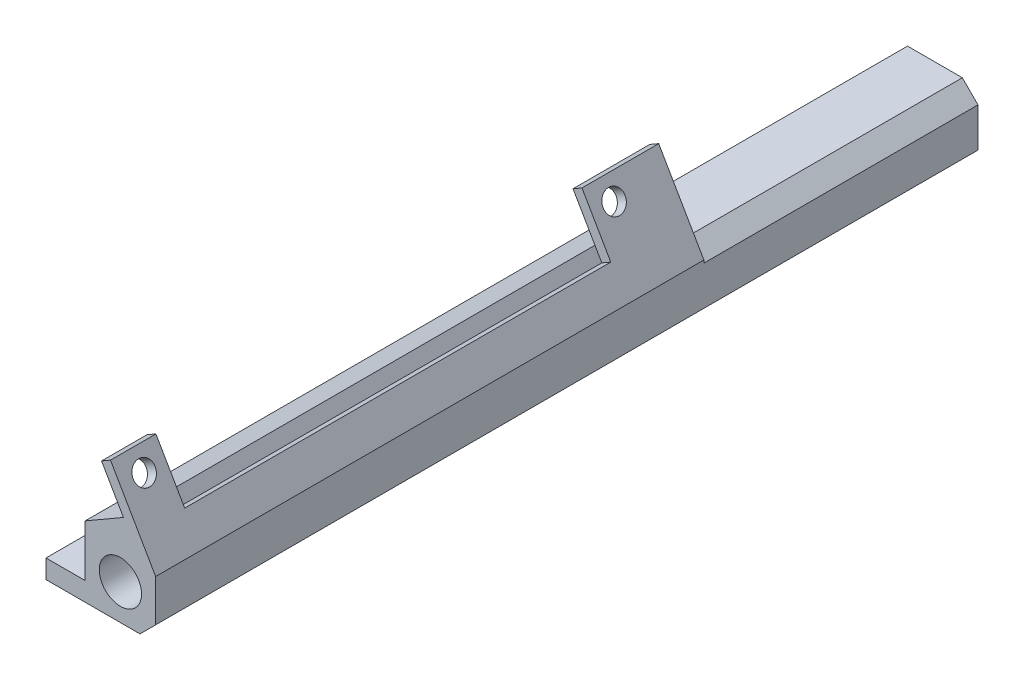
SolidWorks part; units mm, degrees
other "Markup1"
sketch "Sketch18" plane through (59.69, 0, 0) normal (0, 0, 1) x (1, 0, 0)
sketch "Sketch20" plane through (59.69, 0, 0) normal (0, 0, 1) x (1, 0, 0)
sketch "Sketch23" plane through (59.69, 0, 0) normal (0, 0, 1) x (1, 0, 0)
other "Markup2"
sketch "Sketch19" plane through (59.69, 0, 0) normal (0, 0, 1) x (1, 0, 0)
sketch "Sketch21" plane through (59.69, 0, 0) normal (0, 0, 1) x (1, 0, 0)
sketch "Sketch24" plane through (59.69, 0, 0) normal (0, 0, 1) x (1, 0, 0)
ref_plane "Front Plane" through (0, 0, 0) normal (0, 0, 1) x (1, 0, 0)
ref_plane "Top Plane" through (0, 0, 0) normal (0, 1, 0) x (1, 0, 0)
ref_plane "Right Plane" through (0, 0, 0) normal (1, 0, 0) x (0, 0, -1)
sketch "Sketch1" plane through (0, 0, 0) normal (0, 1, 0) x (1, 0, 0)
  line L1 (0, 0) -> (77.47, 0)
  line L2 (0, 0) -> (0, 133.35)
  line L3 (0, 133.35) -> (77.47, 133.35)
  line L4 (77.47, 0) -> (77.47, 133.35)
  dimension "D1" = 77.47
  dimension "D2" = 133.35
extrude "Boss-Extrude1" add sketch "Sketch1" along normal blind 11.43
sketch "Sketch2" plane through (0, 0, 0) normal (0, 0, 1) x (1, 0, 0)
  line L0 (5.715, 5.715) -> (71.755, 5.715) construction
  line L1 (38.735, 11.43) -> (38.735, 0) construction
  line L2 (0, 11.43) -> (77.47, 11.43) construction
  line L3 (0, 0) -> (77.47, 0) construction
  circle A0 centre (5.715, 5.715) radius 3.429
  circle A1 centre (71.755, 5.715) radius 3.429
  point P10 (38.735, 5.715)
  dimension "D1" = 6.858
  dimension "D2" = 66.04
extrude "Cut-Extrude1" cut sketch "Sketch2" against normal through all
sketch "Sketch3" plane through (0, 11.43, 0) normal (0, 1, 0) x (1, 0, 0)
  line L0 (11.43, 133.35) -> (11.43, 95.25)
  line L1 (77.47, 133.35) -> (0, 133.35) construction
  line L2 (11.43, 133.35) -> (66.04, 133.35)
  line L3 (66.04, 133.35) -> (66.04, 95.25)
  line L4 (53.34, 82.55) -> (24.13, 82.55)
  line L5 (0, 133.35) -> (0, 0) construction
  arc A0 (66.04, 95.25) -> (53.34, 82.55) centre (53.34, 95.25) cw
  arc A1 (24.13, 82.55) -> (11.43, 95.25) centre (24.13, 95.25) cw
  point P10 (38.735, 133.35)
  dimension "D1" = 12.7
  dimension "D2" = 11.43
  dimension "D3" = 50.8
extrude "Cut-Extrude2" cut sketch "Sketch3" against normal through all
sketch "Sketch4" plane through (0, 0, -133.35) normal (0, 0, -1) x (-1, 0, 0)
  line L0 (-11.43, 0) -> (-11.43, 11.43) construction
  line L1 (-66.04, 11.43) -> (-11.43, 11.43)
  line L2 (-66.04, 11.43) -> (-66.04, 5.08)
  line L3 (-66.04, 5.08) -> (-11.43, 5.08)
  line L4 (-11.43, 11.43) -> (-11.43, 5.08)
  line L5 (-11.43, 0) -> (0, 0) construction
  dimension "D1" = 5.08
extrude "Cut-Extrude3" cut sketch "Sketch4" against normal through all
chamfer "Chamfer1" distance 2.54 angle 45 4 edges at (0, 0, -66.675) (0, 11.43, -66.675) (77.47, 0, -66.675) (77.47, 11.43, -66.675)
sketch "Sketch5" plane through (0, 11.43, 0) normal (0, 1, 0) x (1, 0, 0)
  line L0 (66.04, 82.55) -> (0, 82.55)
  line L1 (66.04, 0) -> (66.04, 95.25) construction
  line L2 (0, 0) -> (0, 133.35) construction
  line L3 (0, 82.55) -> (0, 133.35)
  line L4 (0, 133.35) -> (66.04, 133.35)
  line L5 (66.04, 133.35) -> (66.04, 82.55)
  line L6 (24.13, 82.55) -> (53.34, 82.55) construction
extrude "Cut-Extrude4" cut sketch "Sketch5" against normal through all
sketch "Sketch6" plane through (0, 11.43, 0) normal (0, 1, 0) x (1, 0, 0)
  line L0 (53.34, 82.55) -> (53.34, 0)
  line L1 (11.43, 82.55) -> (66.04, 82.55) construction
  line L2 (66.04, 0) -> (11.43, 0) construction
  line L3 (53.34, 0) -> (0, 0)
  line L4 (0, 0) -> (0, 82.55)
  line L5 (0, 82.55) -> (53.34, 82.55)
  line L6 (66.04, 0) -> (66.04, 133.35) construction
  dimension "D1" = 12.7
extrude "Cut-Extrude5" cut sketch "Sketch6" against normal through all
sketch "Sketch7" plane through (0, 5.08, 0) normal (0, 1, 0) x (1, 0, 0)
  line L0 (53.34, 82.55) -> (66.04, 82.55) construction
  line L1 (66.04, 0) -> (66.04, 82.55) construction
  circle A0 centre (62.23, 74.93) radius 1.778
  circle A4 centre (62.23, 13.97) radius 1.778
  dimension "D1" = 3.556
  dimension "D2" = 7.62
  dimension "D3" = 68.58
  dimension "D4" = 3.81
extrude "Hole Cuts 1" cut sketch "Sketch7" against normal through all
sketch "Sketch8" plane through (0, 0, 0) normal (0, 0, 1) x (1, 0, 0)
  line L0 (77.47, 11.8699) -> (77.47, 8.89)
  line L1 (77.47, 11.8699) -> (71.882, 21.5486)
  line L2 (71.882, 21.5486) -> (68.6183, 19.6643)
  line L3 (68.6183, 19.6643) -> (71.5393, 14.605)
  line L4 (71.5393, 14.605) -> (66.04, 11.43)
  line L5 (77.47, 11.43) -> (68.58, 11.43) construction
  line L6 (66.04, 11.43) -> (74.93, 11.43) construction
  line L7 (66.04, 11.43) -> (74.93, 11.43)
  line L9 (77.47, 8.89) -> (77.47, 2.54) construction
  line L10 (74.93, 11.43) -> (77.47, 8.89)
  dimension "D2" = 11.176
  dimension "D3" = 6.35
  dimension "D4" = 5.842
  dimension "D6" = 60
extrude "Boss-Extrude2" add sketch "Sketch8" against normal blind 88.9
sketch "Sketch9" plane through (0, 0, 0) normal (0, 0, 1) x (1, 0, 0)
  line L0 (74.93, 0) -> (66.04, 0) construction
  line L1 (53.34, 0) -> (74.93, 0) construction
  line L3 (66.04, 0) -> (59.69, 0) construction
  line L4 (59.69, 0) -> (53.34, 0)
  line L5 (53.34, 0) -> (53.34, 5.08)
  line L6 (53.34, 5.08) -> (59.69, 5.08)
  line L7 (66.04, 5.08) -> (53.34, 5.08) construction
  line L8 (59.69, 5.08) -> (59.69, 0)
  dimension "D1" = 6.35
extrude "Cut-Extrude7" cut sketch "Sketch9" against normal up to next
sketch "Sketch10" plane through (0, 0, 0) normal (0, 0, 1) x (1, 0, 0)
  line L0 (59.69, 5.08) -> (66.04, 5.08)
  line L1 (66.04, 5.08) -> (66.04, 3.81)
  line L2 (66.04, 3.81) -> (59.69, 3.81)
  line L3 (59.69, 0) -> (59.69, 5.08) construction
  line L4 (59.69, 3.81) -> (59.69, 5.08)
  line L5 (59.69, 0) -> (74.93, 0) construction
  dimension "D1" = 3.81
extrude "Cut-Extrude8" cut sketch "Sketch10" against normal up to next
sketch "Sketch11" plane through (59.9786, 34.6287, 0) normal (-0.866, -0.5, 0) x (0, 0, 1)
  line L0 (-88.9, -23.1213) -> (0, -23.1213) construction
  line L2 (0, -17.2793) -> (0, -23.1213) construction
  circle A0 centre (-3.81, -19.3113) radius 1.778
  circle A1 centre (-80.01, -19.3113) radius 1.778
  dimension "D1" = 3.556
  dimension "D4" = 76.2
  dimension "D3" = 3.81
  dimension "D2" = 3.81
extrude "Hole Cuts 2" cut sketch "Sketch11" against normal up to next
sketch "Sketch12" plane through (63.2423, 36.513, 0) normal (0.866, 0.5, 0) x (0, 0, -1)
  line L1 (88.9, -17.2793) -> (0, -17.2793)
  line L2 (88.9, -17.2793) -> (88.9, -28.4553)
  line L3 (88.9, -28.4553) -> (0, -28.4553)
  line L4 (0, -17.2793) -> (0, -28.4553)
extrude "Cut-Extrude10" cut sketch "Sketch12" against normal blind 1.27
sketch "Sketch22" plane through (0, 0, 0) normal (0, 0, 1) x (1, 0, 0)
  line L0 (-928.245, 5.715) -> (49071.755, 5.715) construction
  line L1 (71.755, 5.715) -> (64.2465, 18.7201) construction
  line L2 (64.9306, 17.5352) -> (69.33, 20.0752)
  line L3 (64.9306, 17.5352) -> (67.8516, 12.4759)
  line L4 (69.33, 20.0752) -> (72.251, 15.0159)
  line L5 (67.8516, 12.4759) -> (72.251, 15.0159)
  line L6 (70.7821, 20.9136) -> (68.6183, 19.6643) construction
  line L7 (71.5393, 14.605) -> (66.04, 11.43) construction
  dimension "D1" = 60
  dimension "D2" = 5.08
extrude "Cut-Extrude15" cut sketch "Sketch22" against normal through all
sketch "Sketch14" plane through (0, 3.81, 0) normal (0, 1, 0) x (1, 0, 0)
  line L1 (59.69, 82.55) -> (66.04, 82.55)
  line L2 (59.69, 82.55) -> (59.69, 0)
  line L3 (59.69, 0) -> (66.04, 0)
  line L4 (66.04, 82.55) -> (66.04, 0)
extrude "Cut-Extrude12" cut sketch "Sketch14" against normal blind 0.762
sketch "Sketch15" plane through (8.6397, -14.9643, 0) normal (-0.5, 0.866, 0) x (0.866, 0.5, 0)
  line L1 (71.756, 0) -> (70.0792, 0)
  line L2 (71.756, 0) -> (71.756, 88.9)
  line L3 (71.756, 88.9) -> (70.0792, 88.9)
  line L4 (70.0792, 0) -> (70.0792, 88.9)
extrude "Boss-Extrude3" add sketch "Sketch15" along normal blind 1.27
sketch "Sketch16" plane through (60.6903, 35.0396, 0) normal (-0.866, -0.5, 0) x (0, 0, 1)
  line L0 (-80.01, -19.3113) -> (-3.81, -19.3113) construction
  line L1 (-88.9, -16.0093) -> (0, -16.0093) construction
  line L2 (-76.454, -16.0093) -> (-7.366, -16.0093)
  line L3 (-76.454, -16.0093) -> (-76.454, -25.3438)
  line L4 (-76.454, -25.3438) -> (-7.366, -25.3438)
  line L5 (-7.366, -16.0093) -> (-7.366, -25.3438)
  point P12 (-41.91, -19.3113)
  point P13 (-41.91, -16.0093)
  dimension "D1" = 69.088
  dimension "D2" = 9.3345
extrude "Cut-Extrude13" cut sketch "Sketch16" against normal up to next
sketch "Sketch17" plane through (14.2277, -24.643, 0) normal (-0.5, 0.866, 0) x (0.866, 0.5, 0)
  line L1 (71.756, 88.9) -> (73.026, 88.9)
  line L2 (71.756, 88.9) -> (71.756, 0)
  line L3 (71.756, 0) -> (73.026, 0)
  line L4 (73.026, 88.9) -> (73.026, 0)
extrude "Cut-Extrude14" cut sketch "Sketch17" against normal up to next
